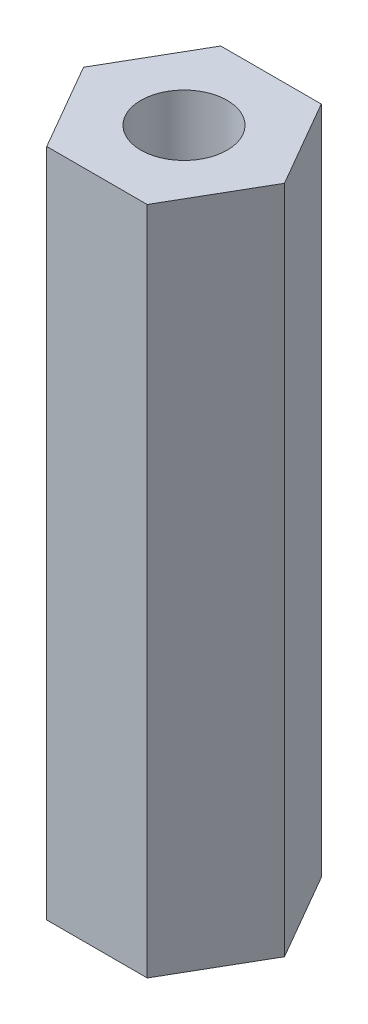
SolidWorks part; units mm, degrees
material "5052-H32"
ref_plane "Front Plane" through (0, 0, 0) normal (0, 0, 1) x (1, 0, 0)
ref_plane "Top Plane" through (0, 0, 0) normal (0, 1, 0) x (1, 0, 0)
ref_plane "Right Plane" through (0, 0, 0) normal (1, 0, 0) x (0, 0, -1)
sketch "Sketch2" plane through (0, 0, 0) normal (0, 1, 0) x (1, 0, 0)
  line L1 (3, 0) -> (1.5, 2.5981)
  line L2 (1.5, 2.5981) -> (-1.5, 2.5981)
  line L3 (-1.5, 2.5981) -> (-3, 0)
  line L4 (-3, 0) -> (-1.5, -2.5981)
  line L5 (-1.5, -2.5981) -> (1.5, -2.5981)
  line L6 (1.5, -2.5981) -> (3, 0)
  circle A1 centre (0, 0) radius 3 construction
extrude "Boss-Extrude1" add sketch "Sketch2" along normal blind 30
hole_wizard "#5-40 Tapped Hole1" positions "Sketch3" profile "Sketch4" tap size "#5-40" standard "ANSI Inch"
sketch "Sketch3" plane through (0, 30, 0) normal (0, 1, 0) x (1, 0, 0)
  point P0 (0, 0)
sketch "Sketch4" plane through (0, 30, 0) normal (1, 0, 0) x (0, 0, 1)
  line L0 (0, 0) -> (0, 15.7745)
  line L1 (0, 15.7745) -> (1.289, 15)
  line L2 (1.289, 15) -> (1.289, 0.7833)
  line L3 (1.289, 0.7833) -> (2.2225, 0)
  line L5 (2.2225, 0) -> (0, 0)
  line L6 (-1.289, 0.7833) -> (-2.2225, 0) construction
  line L10 (0, 15.7745) -> (-1.2891, 15) construction
  line L11 (0, -6.35) -> (0, 107.95) construction
  dimension "Tap Drill Dia." = 2.5781
  dimension "Tap Drill Depth" = 15
  dimension "Near C'Sink Dia." = 4.445
  dimension "Near C'Sink Angle" = 100
  dimension "Drill Angle" = 118
cosmetic thread "Hole Thread1" parameters "D1"=15, "D2"=3.175
sketch "Sketch6" plane through (0, 0, 0) normal (0, -1, 0) x (1, 0, 0)
  line L0 (-1.5, -2.5981) -> (1.5, 2.5981) construction
  line L1 (-1.5, 2.5981) -> (1.5, -2.5981) construction
  line L2 (-3, 0) -> (3, 0) construction
hole_wizard "M4x0.7 Tapped Hole1" positions "3DSketch4" profile "Sketch8" tap size "M4x0.7" standard "ANSI Metric"
sketch3d "3DSketch4"
  line L0 (-1.5, 0, -2.5981) -> (1.5, 0, 2.5981) construction
  point P0 (0, 0, 0)
  point P3 (-0.0145, 0, -0.0251)
sketch "Sketch8" plane through (-0.0145, 0, -0.0251) normal (1, 0, 0) x (0, 0, -1)
  line L0 (0, 0) -> (0, 15.9914)
  line L1 (0, 15.9914) -> (1.65, 15)
  line L2 (1.65, 15) -> (1.65, 0)
  line L5 (1.65, 0) -> (0, 0)
  line L10 (0, 15.9914) -> (-1.65, 15) construction
  line L11 (0, -6.35) -> (0, 107.95) construction
  dimension "Tap Drill Dia." = 3.3
  dimension "Tap Drill Depth" = 15
  dimension "Drill Angle" = 118
cosmetic thread "Hole Thread3" parameters "D1"=15, "D2"=4
sketch "Sketch9" plane through (0, 30, 0) normal (0, 1, 0) x (1, 0, 0)
  circle A0 centre (0, 0) radius 3
extrude "Cut-Extrude2" cut sketch "Sketch9" against normal blind 5 contours A0
sketch "Sketch10" plane through (0, 0, 0) normal (0, -1, 0) x (1, 0, 0)
  circle A0 centre (0, 0) radius 3
extrude "Cut-Extrude3" cut sketch "Sketch10" against normal blind 5
